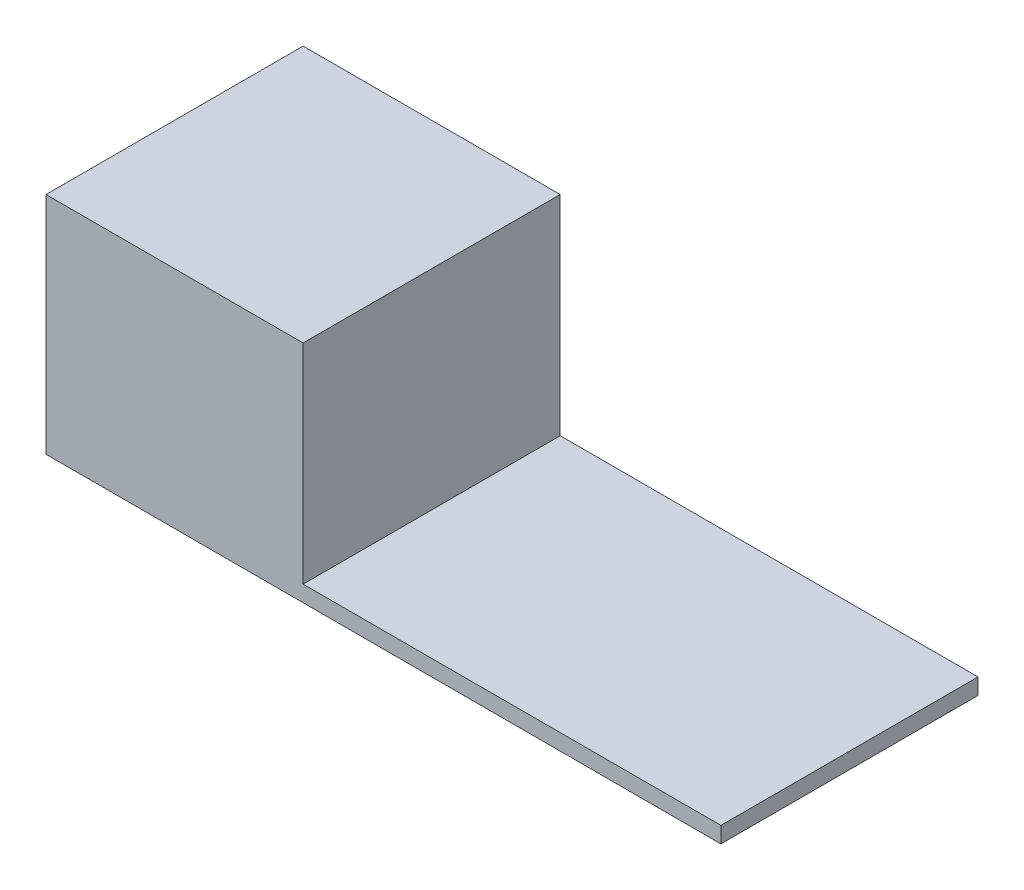
SolidWorks part; units mm, degrees
ref_plane "Front Plane" through (0, 0, 0) normal (0, 0, 1) x (1, 0, 0)
ref_plane "Top Plane" through (0, 0, 0) normal (0, 1, 0) x (1, 0, 0)
ref_plane "Right Plane" through (0, 0, 0) normal (1, 0, 0) x (0, 0, -1)
sketch "Sketch1" plane through (0, 0, 0) normal (0, 1, 0) x (1, 0, 0)
  line L1 (-17.9133, -5.8563) -> (3.0867, -5.8563)
  line L2 (-17.9133, -5.8563) -> (-17.9133, 2.1437)
  line L3 (-17.9133, 2.1437) -> (3.0867, 2.1437)
  line L4 (3.0867, -5.8563) -> (3.0867, 2.1437)
extrude "Boss-Extrude1" add sketch "Sketch1" along normal blind 0.5
sketch "Sketch2" plane through (0, 0.5, 0) normal (0, 1, 0) x (1, 0, 0)
  line L0 (3.0867, 2.1437) -> (-17.9133, 2.1437) construction
  line L1 (-17.9133, -5.8563) -> (-9.9133, -5.8563)
  line L2 (-17.9133, -5.8563) -> (-17.9133, 2.1437)
  line L3 (-17.9133, 2.1437) -> (-9.9133, 2.1437)
  line L4 (-9.9133, -5.8563) -> (-9.9133, 2.1437)
extrude "Boss-Extrude2" add sketch "Sketch2" along normal blind 6.5
